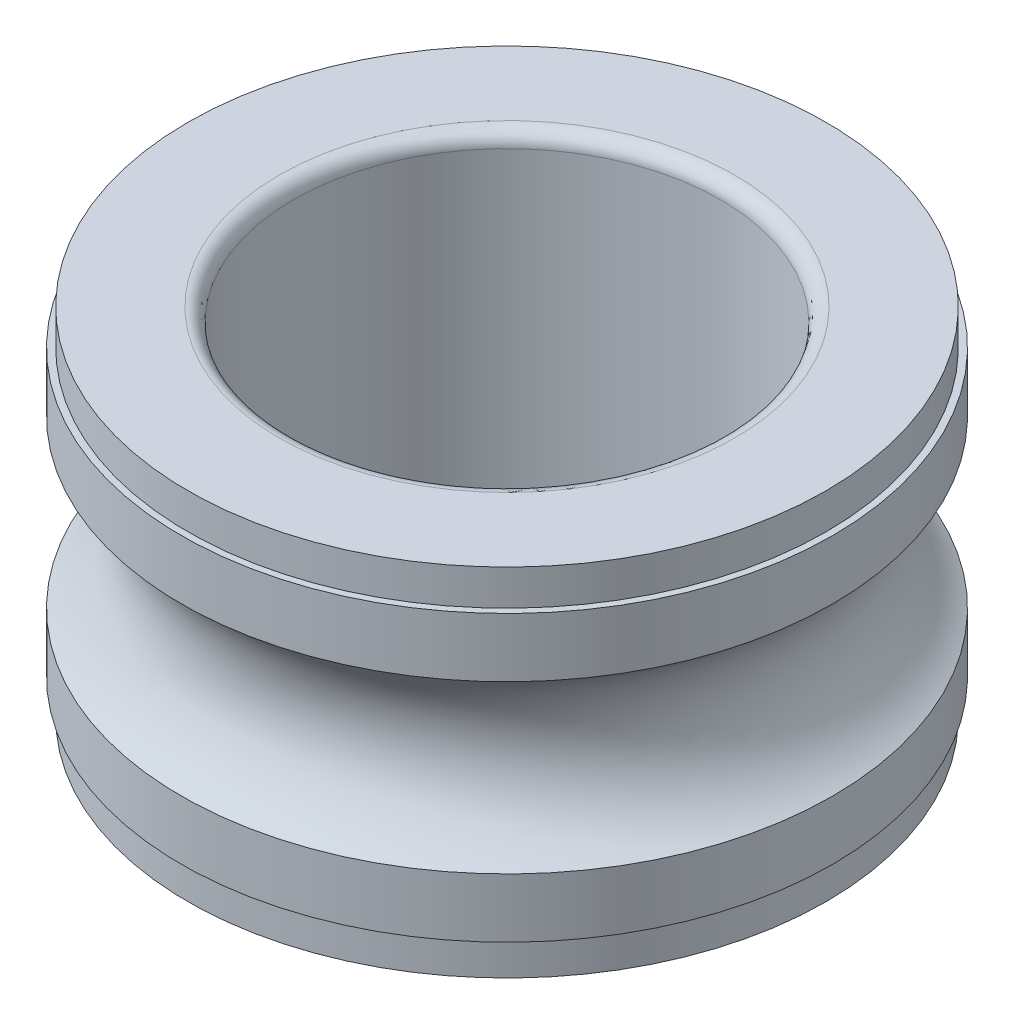
SolidWorks part; units mm, degrees
ref_plane "Front Plane" through (0, 0, 0) normal (0, 0, 1) x (1, 0, 0)
ref_plane "Top Plane" through (0, 0, 0) normal (0, 1, 0) x (1, 0, 0)
ref_plane "Right Plane" through (0, 0, 0) normal (1, 0, 0) x (0, 0, -1)
ref_plane "Plane1" through (0, 0, 0) normal (0, 0, -1) x (-1, 0, 0)
sketch "Sketch1" plane through (0, 0, 0) normal (0, 0, -1) x (-1, 0, 0)
  line L0 (-4.575, -0.5) -> (-4.575, -1.3309)
  line L1 (-4.575, -3.6691) -> (-4.575, -4.5)
  line L2 (-4.575, -4.5) -> (-4.4835, -4.5)
  line L3 (-4.4835, -4.5) -> (-4.4835, -5)
  line L4 (-4.4835, -5) -> (-3.2, -5)
  line L5 (-3, -4.8) -> (-3, -0.2)
  line L6 (-3.2, 0) -> (-4.4835, 0)
  line L7 (-4.4835, 0) -> (-4.4835, -0.5)
  line L8 (-4.4835, -0.5) -> (-4.575, -0.5)
  line L9 (0, -5.0035) -> (0, 0.0035) construction
  arc A0 (-4.575, -1.3309) -> (-4.575, -3.6691) centre (-5.25, -2.5) cw
  arc A1 (-3.2, -5) -> (-3, -4.8) centre (-3.2, -4.8) ccw
  arc A2 (-3, -0.2) -> (-3.2, 0) centre (-3.2, -0.2) ccw
revolve "Revolve1" add sketch "Sketch1" angle 360 about L9
